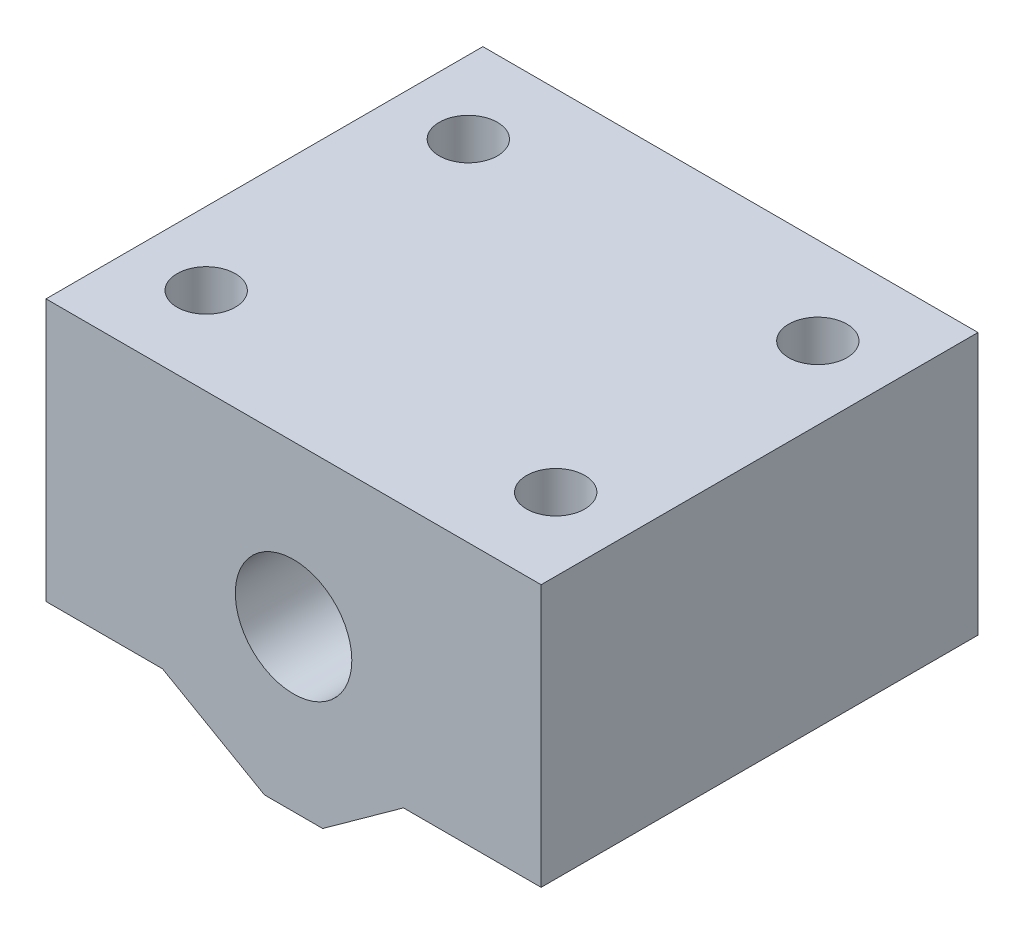
SolidWorks part; units mm, degrees
ref_plane "Front Plane" through (0, 0, 0) normal (0, 0, 1) x (1, 0, 0)
ref_plane "Top Plane" through (0, 0, 0) normal (0, 1, 0) x (1, 0, 0)
ref_plane "Right Plane" through (0, 0, 0) normal (1, 0, 0) x (0, 0, -1)
sketch "Sketch1" plane through (0, 0, 0) normal (0, 0, 1) x (1, 0, 0)
  line L0 (0, 0) -> (34, 0)
  line L1 (34, 0) -> (34, -18)
  line L3 (0, -18) -> (0, 0)
  line L5 (17, -22) -> (13, -22)
  line L6 (0, -18) -> (5, -18)
  line L7 (5, -18) -> (13, -22)
  line L8 (17, -22) -> (21, -22)
  line L9 (34, -18) -> (27.548, -18)
  line L10 (27.548, -18) -> (21, -22)
  circle A0 centre (17, -11) radius 4
sketch "Sketch2" plane through (0, 0, 0) normal (0, 0, 1) x (1, 0, 0)
  line L0 (0, 0) -> (34, 0)
  line L1 (34, 0) -> (34, -18)
  line L2 (0, -18) -> (0, 0)
  line L3 (17, -22) -> (15, -22)
  line L4 (0, -18) -> (5, -18)
  line L6 (17, -22) -> (19, -22)
  line L7 (34, -18) -> (27.548, -18)
  line L9 (5, -18) -> (8, -18)
  line L10 (8, -18) -> (15, -22)
  line L11 (27.548, -18) -> (24.548, -18)
  line L12 (24.548, -18) -> (19, -22)
  circle A0 centre (17, -11) radius 4
extrude "Boss-Extrude1" add sketch "Sketch2" along normal blind 30
sketch "Sketch4" plane through (0, -18, 0) normal (0, -1, 0) x (1, 0, 0)
  line L0 (0, 30) -> (0, 0) construction
  line L1 (34, 30) -> (34, 0) construction
  circle A0 centre (5, 6) radius 2
  circle A1 centre (29, 6) radius 2
  circle A2 centre (5, 24) radius 2
  circle A3 centre (29, 24) radius 2
  dimension "D1" = 5
  dimension "D2" = 5
  dimension "D3" = 5
  dimension "D4" = 5
extrude "Cut-Extrude1" cut sketch "Sketch4" against normal through all
